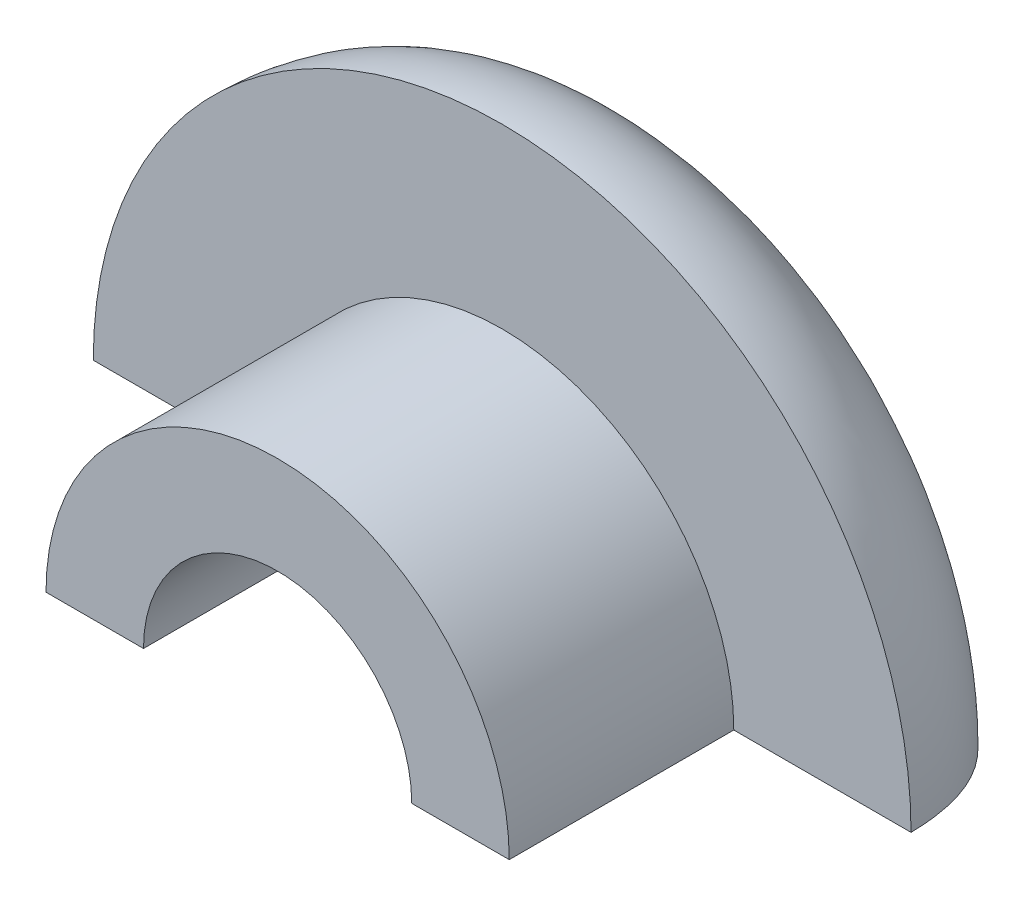
SolidWorks part; units mm, degrees
ref_plane "Front Plane" through (0, 0, 0) normal (0, 0, 1) x (1, 0, 0)
ref_plane "Top Plane" through (0, 0, 0) normal (0, 1, 0) x (1, 0, 0)
ref_plane "Right Plane" through (0, 0, 0) normal (1, 0, 0) x (0, 0, -1)
sketch "Sketch1" plane through (0, 0, 0) normal (0, 0, 1) x (1, 0, 0)
  circle A0 centre (0, 0) radius 4.9784
  dimension "D1" = 9.9568
extrude "Boss-Extrude1" add sketch "Sketch1" along normal blind 4.826
sketch "Sketch3" plane through (0, 0, 0) normal (1, 0, 0) x (0, 0, -1)
  line L0 (0, 0) -> (6.35, 0)
  line L1 (0, 0) -> (0, 4.9784)
  line L2 (0, 4.9784) -> (0, 8.7884)
  spline S0 degree 3 poles (0, 8.7884) (2.7955, 8.7439) (3.1945, 4.5572) (6.5004, 2.1374) (6.35, 0) knots 0 0 0 0 0.503114 1 1 1 1
  dimension "D1" = 6.35
  dimension "D2" = 3.81
revolve "Revolve1" add sketch "Sketch3" angle 360 about L0
sketch "Sketch2" plane through (0, 0, 0) normal (0, 0, 1) x (1, 0, 0)
  circle A0 centre (0, 0) radius 2.8829
  dimension "D1" = 5.7658
extrude "Cut-Extrude1" cut sketch "Sketch2" against normal through all both and the other way through all
ref_plane "Plane1" through (0, 0, -5.405) normal (0, 0, 1) x (1, 0, 0)
sketch "Sketch5" plane through (0, 0, -5.405) normal (0, 0, 1) x (1, 0, 0)
  circle A0 centre (0, 0) radius 6.35
  dimension "D1" = 12.7
extrude "Cut-Extrude4" cut sketch "Sketch5" along normal blind 0.762 contours A0
sketch "Sketch8" plane through (0, 0, 0) normal (0, 1, 0) x (1, 0, 0)
  line L1 (-12.7, 12.7) -> (12.7, 12.7)
  line L2 (-12.7, 12.7) -> (-12.7, -12.7)
  line L3 (-12.7, -12.7) -> (12.7, -12.7)
  line L4 (12.7, 12.7) -> (12.7, -12.7)
  line L5 (-12.7, 12.7) -> (12.7, -12.7) construction
  line L6 (-12.7, -12.7) -> (12.7, 12.7) construction
  point P0 (0, 0)
  dimension "D1" = 25.4
  dimension "D2" = 25.4
extrude "Cut-Extrude5" cut sketch "Sketch8" against normal through all
